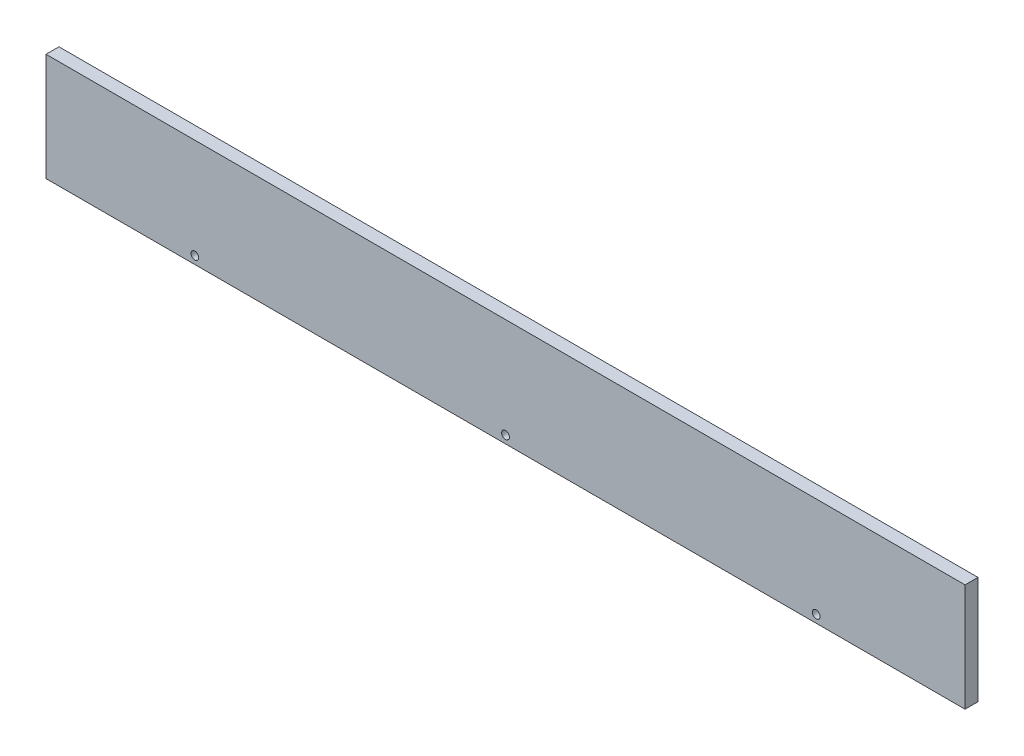
SolidWorks part; units mm, degrees
ref_plane "Front Plane" through (0, 0, 0) normal (0, 0, 1) x (1, 0, 0)
ref_plane "Top Plane" through (0, 0, 0) normal (0, 1, 0) x (1, 0, 0)
ref_plane "Right Plane" through (0, 0, 0) normal (1, 0, 0) x (0, 0, -1)
sketch "Sketch1" plane through (0, 0, 0) normal (0, 0, 1) x (1, 0, 0)
  line L1 (0, 0) -> (450.85, 0)
  line L2 (0, 0) -> (0, -52.832)
  line L3 (0, -52.832) -> (450.85, -52.832)
  line L4 (450.85, 0) -> (450.85, -52.832)
  dimension "D1" = 52.832
  dimension "D2" = 450.85
extrude "Boss-Extrude1" add sketch "Sketch1" along normal blind 6.35
sketch "Sketch2" plane through (0, 0, 6.35) normal (0, 0, 1) x (1, 0, 0)
  line L0 (0, -52.832) -> (450.85, -52.832) construction
  circle A0 centre (73.025, -49.022) radius 1.905
  circle A1 centre (225.425, -49.022) radius 1.905
  circle A2 centre (377.825, -49.022) radius 1.905
  point P8 (225.425, -52.832)
  dimension "D1" = 3.81
  dimension "D2" = 152.4
  dimension "D3" = 152.4
  dimension "D4" = 3.81
extrude "Cut-Extrude1" cut sketch "Sketch2" against normal blind 6.35
